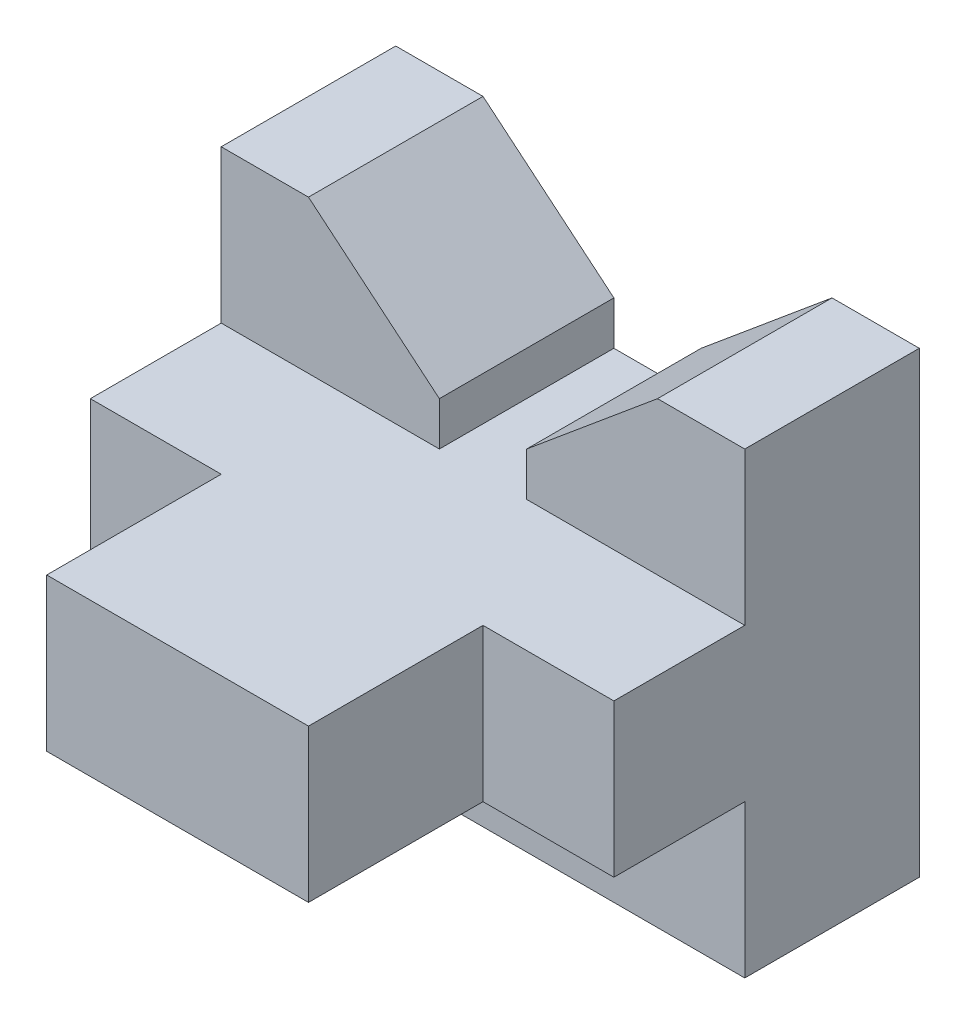
SolidWorks part; units mm, degrees
ref_plane "Front Plane" through (0, 0, 0) normal (0, 0, 1) x (1, 0, 0)
ref_plane "Top Plane" through (0, 0, 0) normal (0, 1, 0) x (1, 0, 0)
ref_plane "Right Plane" through (0, 0, 0) normal (1, 0, 0) x (0, 0, -1)
sketch "Sketch1" plane through (0, 0, 0) normal (1, 0, 0) x (0, 0, -1)
  line L0 (-10.0584, -30.4038) -> (8.9916, -30.4038)
  line L1 (34.3916, 14.0462) -> (34.3916, -52.6288)
  line L2 (34.3916, 14.0462) -> (8.9916, 14.0462)
  line L3 (8.9916, 14.0462) -> (8.9916, -8.1788)
  line L4 (8.9916, -8.1788) -> (-10.0584, -8.1788)
  line L5 (-10.0584, -8.1788) -> (-10.0584, -30.4038)
  line L6 (8.9916, -30.4038) -> (8.9916, -52.6288)
  line L7 (8.9916, -52.6288) -> (34.3916, -52.6288)
  point P1 (34.3916, -19.2913)
  dimension "D1" = 19.05
  dimension "D2" = 25.4
  dimension "D3" = 66.675
  dimension "D4" = 22.225
  dimension "D5" = 22.225
extrude "Boss-Extrude1" add sketch "Sketch1" along normal mid plane 76.2
sketch "Sketch2" plane through (0, 0, 10.0584) normal (0, 0, 1) x (1, 0, 0)
  line L0 (38.1, -8.1788) -> (-38.1, -8.1788) construction
  line L1 (-19.05, -8.1788) -> (19.05, -8.1788)
  line L2 (-19.05, -8.1788) -> (-19.05, -30.4038)
  line L3 (-19.05, -30.4038) -> (19.05, -30.4038)
  line L4 (19.05, -8.1788) -> (19.05, -30.4038)
  line L5 (38.1, -30.4038) -> (-38.1, -30.4038) construction
  line L6 (0, -24.4475) -> (0, 24.4475) construction
  line L7 (38.1, -8.1788) -> (38.1, -30.4038) construction
  point P8 (0, -8.1788)
  dimension "D1" = 19.05
extrude "Boss-Extrude2" add sketch "Sketch2" along normal blind 25.4
sketch "Sketch3" plane through (0, 0, -8.9916) normal (0, 0, 1) x (1, 0, 0)
  line L0 (38.1, 14.0462) -> (38.1, -8.1788)
  line L1 (38.1, -8.1788) -> (6.35, -8.1788)
  line L2 (38.1, -8.1788) -> (-38.1, -8.1788) construction
  line L3 (6.35, -8.1788) -> (6.35, -1.8288)
  line L4 (6.35, -1.8288) -> (25.4, 14.0462)
  line L5 (38.1, 14.0462) -> (-38.1, 14.0462) construction
  line L6 (25.4, 14.0462) -> (38.1, 14.0462)
  line L7 (-38.1, -8.1788) -> (-6.35, -8.1788)
  line L8 (-6.35, -8.1788) -> (-6.35, -1.8288)
  line L9 (-6.35, -1.8288) -> (-25.4, 14.0462)
  line L10 (-25.4, 14.0462) -> (-38.1, 14.0462)
  line L11 (-38.1, 14.0462) -> (-38.1, -8.1788)
  line L12 (0, -36.6713) -> (0, 36.6713) construction
  line L13 (-25.4, 14.0462) -> (25.4, 14.0462)
  point P14 (0, 14.0462)
  line M10 (-38.1, -8.1788) -> (38.1, -8.1788)
  line M12 (38.1, 14.0462) -> (-38.1, 14.0462)
  dimension "D1" = 12.7
  dimension "D2" = 6.35
  dimension "D3" = 19.05
extrude "Cut-Extrude1" cut sketch "Sketch3" against normal blind 25.4 contours L9 L8 L3 L4 M10 M12
